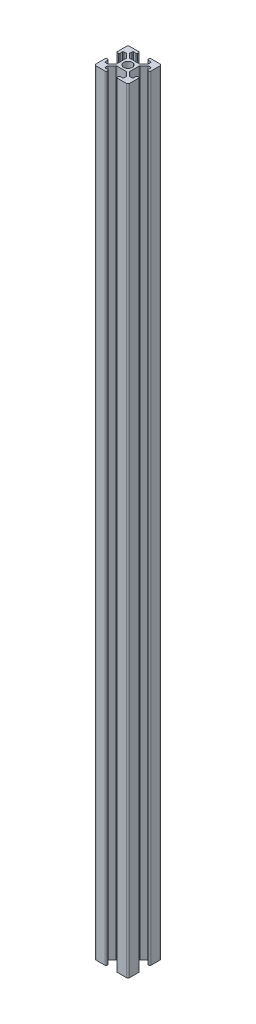
SolidWorks part; units mm, degrees
ref_plane "Front Plane" through (0, 0, 0) normal (0, 0, 1) x (1, 0, 0)
ref_plane "Top Plane" through (0, 0, 0) normal (0, 1, 0) x (1, 0, 0)
ref_plane "Right Plane" through (0, 0, 0) normal (1, 0, 0) x (0, 0, -1)
ref_plane "Plane1" through (0, 230, 0) normal (0, 1, 0) x (1, 0, 0)
sketch "Sketch1" plane through (0, 230, 0) normal (0, 1, 0) x (1, 0, 0)
  line L0 (-3.1, 8.85) -> (-3.1, 9.5)
  line L1 (-3.6, 10) -> (-9, 10)
  line L2 (-10, 9) -> (-10, 3.6)
  line L3 (-9.5, 3.1) -> (-8.85, 3.1)
  line L4 (-8.35, 3.6) -> (-8.35, 5)
  line L5 (-7.85, 5.5) -> (-6.6263, 5.5)
  line L6 (-6.2728, 5.3536) -> (-4.0464, 3.1272)
  line L7 (-3.9, 2.7737) -> (-3.9, -2.7737)
  line L8 (-4.0464, -3.1272) -> (-6.2728, -5.3536)
  line L9 (-6.6263, -5.5) -> (-7.85, -5.5)
  line L10 (-8.35, -5) -> (-8.35, -3.6)
  line L11 (-8.85, -3.1) -> (-9.5, -3.1)
  line L12 (-10, -3.6) -> (-10, -9)
  line L13 (-9, -10) -> (-3.6, -10)
  line L14 (-3.1, -9.5) -> (-3.1, -8.85)
  line L15 (-3.6, -8.35) -> (-5, -8.35)
  line L16 (-5.5, -7.85) -> (-5.5, -6.6263)
  line L17 (-5.3536, -6.2728) -> (-3.1272, -4.0464)
  line L18 (-2.7737, -3.9) -> (2.7737, -3.9)
  line L19 (3.1272, -4.0464) -> (5.3536, -6.2728)
  line L20 (5.5, -6.6263) -> (5.5, -7.85)
  line L21 (5, -8.35) -> (3.6, -8.35)
  line L22 (3.1, -8.85) -> (3.1, -9.5)
  line L23 (3.6, -10) -> (9, -10)
  line L24 (10, -9) -> (10, -3.6)
  line L25 (9.5, -3.1) -> (8.85, -3.1)
  line L26 (8.35, -3.6) -> (8.35, -5)
  line L27 (7.85, -5.5) -> (6.6263, -5.5)
  line L28 (6.2728, -5.3536) -> (4.0464, -3.1272)
  line L29 (3.9, -2.7737) -> (3.9, 2.7737)
  line L30 (4.0464, 3.1272) -> (6.2728, 5.3536)
  line L31 (6.6263, 5.5) -> (7.85, 5.5)
  line L32 (8.35, 5) -> (8.35, 3.6)
  line L33 (8.85, 3.1) -> (9.5, 3.1)
  line L34 (10, 3.6) -> (10, 9)
  line L35 (9, 10) -> (3.6, 10)
  line L36 (3.1, 9.5) -> (3.1, 8.85)
  line L37 (3.6, 8.35) -> (5, 8.35)
  line L38 (5.5, 7.85) -> (5.5, 6.6263)
  line L39 (5.3536, 6.2728) -> (3.1272, 4.0464)
  line L40 (2.7737, 3.9) -> (-2.7737, 3.9)
  line L41 (-3.1272, 4.0464) -> (-5.5, 6.4192)
  line L42 (-5.5, 6.4192) -> (-5.5, 7.85)
  line L43 (-5, 8.35) -> (-3.6, 8.35)
  circle A0 centre (0, 0) radius 2.6
  arc A1 (-3.1, 9.5) -> (-3.6, 10) centre (-3.6, 9.5) ccw
  arc A2 (-9, 10) -> (-10, 9) centre (-9, 9) ccw
  arc A3 (-10, 3.6) -> (-9.5, 3.1) centre (-9.5, 3.6) ccw
  arc A4 (-8.85, 3.1) -> (-8.35, 3.6) centre (-8.85, 3.6) ccw
  arc A5 (-8.35, 5) -> (-7.85, 5.5) centre (-7.85, 5) cw
  arc A6 (-6.6263, 5.5) -> (-6.2728, 5.3536) centre (-6.6263, 5) cw
  arc A7 (-4.0464, 3.1272) -> (-3.9, 2.7737) centre (-4.4, 2.7737) cw
  arc A8 (-3.9, -2.7737) -> (-4.0464, -3.1272) centre (-4.4, -2.7737) cw
  arc A9 (-6.2728, -5.3536) -> (-6.6263, -5.5) centre (-6.6263, -5) cw
  arc A10 (-7.85, -5.5) -> (-8.35, -5) centre (-7.85, -5) cw
  arc A11 (-8.35, -3.6) -> (-8.85, -3.1) centre (-8.85, -3.6) ccw
  arc A12 (-9.5, -3.1) -> (-10, -3.6) centre (-9.5, -3.6) ccw
  arc A13 (-10, -9) -> (-9, -10) centre (-9, -9) ccw
  arc A14 (-3.6, -10) -> (-3.1, -9.5) centre (-3.6, -9.5) ccw
  arc A15 (-3.1, -8.85) -> (-3.6, -8.35) centre (-3.6, -8.85) ccw
  arc A16 (-5, -8.35) -> (-5.5, -7.85) centre (-5, -7.85) cw
  arc A17 (-5.5, -6.6263) -> (-5.3536, -6.2728) centre (-5, -6.6263) cw
  arc A18 (-3.1272, -4.0464) -> (-2.7737, -3.9) centre (-2.7737, -4.4) cw
  arc A19 (2.7737, -3.9) -> (3.1272, -4.0464) centre (2.7737, -4.4) cw
  arc A20 (5.3536, -6.2728) -> (5.5, -6.6263) centre (5, -6.6263) cw
  arc A21 (5.5, -7.85) -> (5, -8.35) centre (5, -7.85) cw
  arc A22 (3.6, -8.35) -> (3.1, -8.85) centre (3.6, -8.85) ccw
  arc A23 (3.1, -9.5) -> (3.6, -10) centre (3.6, -9.5) ccw
  arc A24 (9, -10) -> (10, -9) centre (9, -9) ccw
  arc A25 (10, -3.6) -> (9.5, -3.1) centre (9.5, -3.6) ccw
  arc A26 (8.85, -3.1) -> (8.35, -3.6) centre (8.85, -3.6) ccw
  arc A27 (8.35, -5) -> (7.85, -5.5) centre (7.85, -5) cw
  arc A28 (6.6263, -5.5) -> (6.2728, -5.3536) centre (6.6263, -5) cw
  arc A29 (4.0464, -3.1272) -> (3.9, -2.7737) centre (4.4, -2.7737) cw
  arc A30 (3.9, 2.7737) -> (4.0464, 3.1272) centre (4.4, 2.7737) cw
  arc A31 (6.2728, 5.3536) -> (6.6263, 5.5) centre (6.6263, 5) cw
  arc A32 (7.85, 5.5) -> (8.35, 5) centre (7.85, 5) cw
  arc A33 (8.35, 3.6) -> (8.85, 3.1) centre (8.85, 3.6) ccw
  arc A34 (9.5, 3.1) -> (10, 3.6) centre (9.5, 3.6) ccw
  arc A35 (10, 9) -> (9, 10) centre (9, 9) ccw
  arc A36 (3.6, 10) -> (3.1, 9.5) centre (3.6, 9.5) ccw
  arc A37 (3.1, 8.85) -> (3.6, 8.35) centre (3.6, 8.85) ccw
  arc A38 (5, 8.35) -> (5.5, 7.85) centre (5, 7.85) cw
  arc A39 (5.5, 6.6263) -> (5.3536, 6.2728) centre (5, 6.6263) cw
  arc A40 (3.1272, 4.0464) -> (2.7737, 3.9) centre (2.7737, 4.4) cw
  arc A41 (-2.7737, 3.9) -> (-3.1272, 4.0464) centre (-2.7737, 4.4) cw
  arc A42 (-5.5, 7.85) -> (-5, 8.35) centre (-5, 7.85) cw
  arc A43 (-3.6, 8.35) -> (-3.1, 8.85) centre (-3.6, 8.85) ccw
extrude "Boss-Extrude1" add sketch "Sketch1" against normal blind 460
